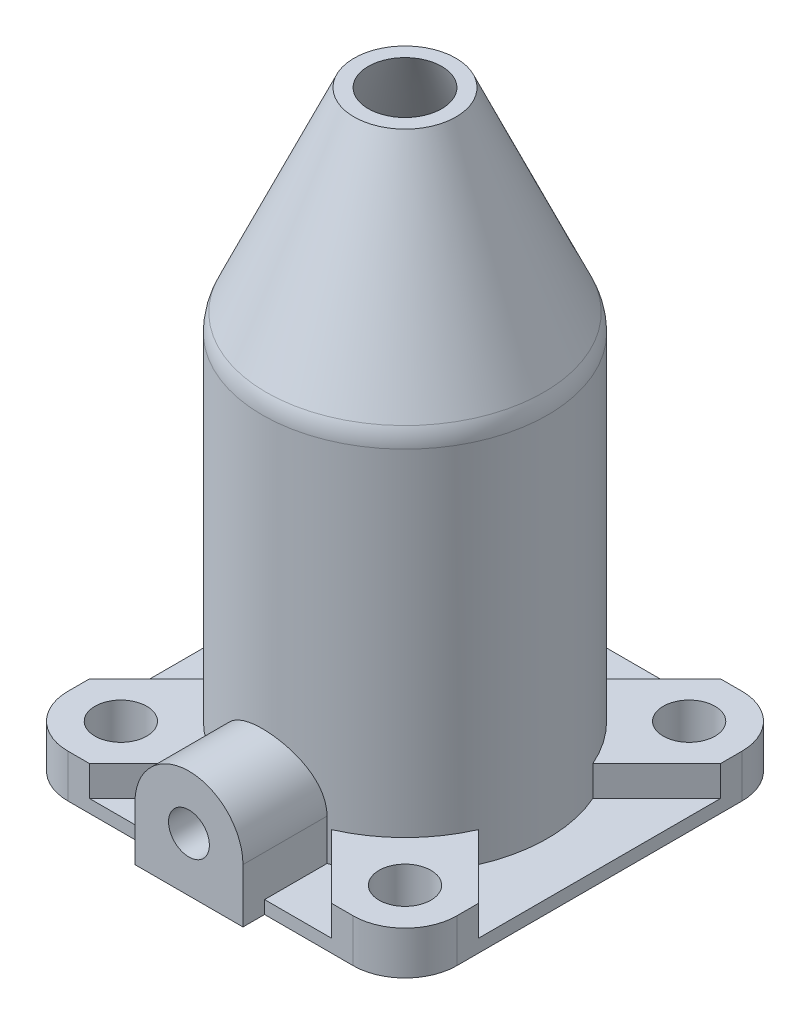
SolidWorks part; units mm, degrees
material "Brass"
ref_plane "Front" through (0, 0, 0) normal (0, 0, 1) x (1, 0, 0)
ref_plane "Top" through (0, 0, 0) normal (0, 1, 0) x (1, 0, 0)
ref_plane "Right" through (0, 0, 0) normal (1, 0, 0) x (0, 0, -1)
sketch "Sketch1" plane through (0, 0, 0) normal (0, 1, 0) x (1, 0, 0)
  line L1 (-33, -45) -> (33, -45)
  line L2 (-45, -33) -> (-45, 33)
  line L3 (-33, 45) -> (33, 45)
  line L4 (45, -33) -> (45, 33)
  line L5 (-45, -45) -> (45, 45) construction
  line L6 (-45, 45) -> (45, -45) construction
  arc A0 (-33, -45) -> (-45, -33) centre (-33, -33) cw
  arc A1 (33, -45) -> (45, -33) centre (33, -33) ccw
  arc A2 (33, 45) -> (45, 33) centre (33, 33) cw
  arc A3 (-45, 33) -> (-33, 45) centre (-33, 33) cw
  point P0 (0, 0)
  dimension "D1" = 12
  dimension "D2" = 12
  dimension "D3" = 12
  dimension "D4" = 12
  dimension "D5" = 90
extrude "Boss-Extrude1" add sketch "Sketch1" along normal blind 3
sketch "Sketch2" plane through (0, 3, 0) normal (0, 1, 0) x (1, 0, 0)
  circle A0 centre (0, 0) radius 30
  dimension "D1" = 60
extrude "Cut-Extrude1" cut sketch "Sketch2" against normal up to surface (3 mm away) up to face at (0, 0, 0)
sketch "Sketch3" plane through (0, 0, 0) normal (0, 0, 1) x (1, 0, 0)
  line L0 (30, 3) -> (30, 89.3545)
  line L1 (-33, 3) -> (33, 3) construction
  line L2 (30, 89.3545) -> (8.5, 137)
  line L3 (8.5, 137) -> (11.7913, 137)
  line L4 (11.7913, 137) -> (33, 90)
  line L5 (33, 90) -> (33, 3)
  line L6 (33, 3) -> (30, 3)
  line L7 (30, 89.3545) -> (32.7345, 90.5884) construction
  line L8 (30, 3) -> (-30, 3) construction
  line L9 (0, -50) -> (0, 50) construction
  line L10 (33, 0) -> (-33, 0) construction
  dimension "D1" = 3
  dimension "D2" = 134
  dimension "D3" = 8.5
  dimension "D4" = 87
  dimension "D5" = 137
  dimension "D6" = 33
revolve "Revolve1" add sketch "Sketch3" angle 360 about axis through (0, -84.8528, 0) along (0, 1, 0)
sketch "Sketch4" plane through (0, 3, 0) normal (0, 1, 0) x (1, 0, 0)
  line L0 (-33, -33) -> (0, 0) construction
  line L1 (-13.2518, -30.2223) -> (-28.0294, -45)
  line L2 (-33, -45) -> (33, -45) construction
  line L3 (-30.2223, -13.2518) -> (-45, -28.0294)
  line L4 (-45, 33) -> (-45, -33) construction
  line L5 (-33, -45) -> (-28.0294, -45)
  line L6 (-45, -28.0294) -> (-45, -33)
  circle A1 centre (0, 0) radius 33 construction
  arc A2 (-45, -33) -> (-33, -45) centre (-33, -33) ccw construction
  arc A3 (-45, -33) -> (-33, -45) centre (-33, -33) ccw
  arc A4 (-30.2223, -13.2518) -> (-13.2518, -30.2223) centre (0, 0) ccw
  dimension "D1" = 24
extrude "Boss-Extrude2" add sketch "Sketch4" along normal blind 7
sketch "Sketch5" plane through (0, 10, 0) normal (0, 1, 0) x (1, 0, 0)
  line L0 (-41.4853, -41.4853) -> (-23.3345, -23.3345) construction
  circle A0 centre (-32.8805, -32.8805) radius 6
  arc A1 (-45, -33) -> (-33, -45) centre (-33, -33) ccw construction
  arc A2 (-30.2223, -13.2518) -> (-13.2518, -30.2223) centre (0, 0) ccw construction
  dimension "D1" = 12
  dimension "D2" = 46.5
extrude "Cut-Extrude2" cut sketch "Sketch5" against normal up to surface (10 mm away) up to face at (0, 0, -30)
pattern_circular "CirPattern1" count 4 over 360 about axis through (0, 0, 0) along (0, 1, 0) of "Boss-Extrude2", "Cut-Extrude2"
sketch "Sketch6" plane through (0, 0, 45) normal (0, 0, 1) x (1, 0, 0)
  line L1 (0, -50) -> (0, 50) construction
  line L3 (-12.5, 12.5) -> (-12.5, 0)
  line L4 (-12.5, 0) -> (12.5, 0)
  line L5 (12.5, 12.5) -> (12.5, 0)
  line L6 (-3.1148, 24.6057) -> (12.5, 0) construction
  line L8 (-12.5, 0) -> (3.1148, 24.6057) construction
  line L9 (50, 0) -> (-50, 0) construction
  arc A0 (12.5, 12.5) -> (-12.5, 12.5) centre (0, 12.5) ccw
  point P0 (0, 19.6975)
  point P4 (0, 25)
  dimension "D2" = 25
  dimension "D1" = 25
extrude "Boss-Extrude3" add sketch "Sketch6" against normal up to body from offset 5 separate body
sketch "Sketch8" plane through (0, 0, 50) normal (0, 0, 1) x (1, 0, 0)
  line L0 (50, 0) -> (-50, 0) construction
  circle A0 centre (0, 12.5) radius 4.725
  dimension "D1" = 9.45
  dimension "D2" = 12.5
extrude "Cut-Extrude3" cut sketch "Sketch8" against normal blind 18 contours A0
sketch "Sketch9" plane through (0, 0, 50) normal (0, 0, 1) x (1, 0, 0)
  line L3 (12.5, 0) -> (12.5, 12.5)
  line L4 (-12.5, 12.5) -> (-12.5, 0)
  line L5 (-12.5, 0) -> (12.5, 0)
  line L6 (12.5, 0) -> (12.5, 12.5)
  line L7 (-12.5, 12.5) -> (-12.5, 0)
  line L8 (-12.5, 0) -> (12.5, 0)
  arc A1 (12.5, 12.5) -> (-12.5, 12.5) centre (0, 12.5) ccw
  arc A2 (12.5, 12.5) -> (-12.5, 12.5) centre (0, 12.5) ccw
  circle A3 centre (0, 12.5) radius 4.725 construction
  circle A4 centre (0, 12.5) radius 4.725
  dimension "D1" = 0
extrude "Boss-Extrude4" [suppressed] add sketch "Sketch9" along normal blind 1.5 separate body
sketch "Sketch10" plane through (0, 10, 0) normal (0, 1, 0) x (1, 0, 0)
  line L4 (-13.2518, 30.2223) -> (-28.0294, 45)
  line L5 (-28.0294, 45) -> (-33, 45)
  line L6 (-45, 33) -> (-45, 28.0294)
  line L7 (-45, 28.0294) -> (-30.2223, 13.2518)
  line L8 (-13.2518, 30.2223) -> (-28.0294, 45)
  line L9 (-28.0294, 45) -> (-33, 45)
  line L10 (-45, 33) -> (-45, 28.0294)
  line L11 (-45, 28.0294) -> (-30.2223, 13.2518)
  line L12 (30.2223, 13.2518) -> (45, 28.0294)
  line L13 (45, 28.0294) -> (45, 33)
  line L14 (33, 45) -> (28.0294, 45)
  line L15 (28.0294, 45) -> (13.2518, 30.2223)
  line L16 (30.2223, 13.2518) -> (45, 28.0294)
  line L17 (45, 28.0294) -> (45, 33)
  line L18 (33, 45) -> (28.0294, 45)
  line L19 (28.0294, 45) -> (13.2518, 30.2223)
  line L20 (13.2518, -30.2223) -> (28.0294, -45)
  line L21 (28.0294, -45) -> (33, -45)
  line L22 (45, -33) -> (45, -28.0294)
  line L23 (45, -28.0294) -> (30.2223, -13.2518)
  line L24 (13.2518, -30.2223) -> (28.0294, -45)
  line L25 (28.0294, -45) -> (33, -45)
  line L26 (45, -33) -> (45, -28.0294)
  line L27 (45, -28.0294) -> (30.2223, -13.2518)
  line L28 (-30.2223, -13.2518) -> (-45, -28.0294)
  line L29 (-45, -28.0294) -> (-45, -33)
  line L30 (-33, -45) -> (-28.0294, -45)
  line L31 (-28.0294, -45) -> (-13.2518, -30.2223)
  line L32 (-30.2223, -13.2518) -> (-45, -28.0294)
  line L33 (-45, -28.0294) -> (-45, -33)
  line L34 (-33, -45) -> (-28.0294, -45)
  line L35 (-28.0294, -45) -> (-13.2518, -30.2223)
  circle A0 centre (32.8805, 32.8805) radius 6 construction
  circle A1 centre (32.8805, -32.8805) radius 6 construction
  arc A2 (-13.2518, 30.2223) -> (-30.2223, 13.2518) centre (0, 0) ccw
  arc A3 (-33, 45) -> (-45, 33) centre (-33, 33) ccw
  arc A4 (-13.2518, 30.2223) -> (-30.2223, 13.2518) centre (0, 0) ccw
  arc A5 (-33, 45) -> (-45, 33) centre (-33, 33) ccw
  circle A6 centre (-32.8805, -32.8805) radius 6 construction
  circle A7 centre (-32.8805, 32.8805) radius 6 construction
  circle A8 centre (32.8805, 32.8805) radius 6
  circle A9 centre (32.8805, -32.8805) radius 6
  circle A10 centre (-32.8805, -32.8805) radius 6
  circle A11 centre (-32.8805, 32.8805) radius 6
  arc A14 (30.2223, 13.2518) -> (13.2518, 30.2223) centre (0, 0) ccw
  arc A15 (45, 33) -> (33, 45) centre (33, 33) ccw
  arc A16 (30.2223, 13.2518) -> (13.2518, 30.2223) centre (0, 0) ccw
  arc A17 (45, 33) -> (33, 45) centre (33, 33) ccw
  arc A18 (13.2518, -30.2223) -> (30.2223, -13.2518) centre (0, 0) ccw
  arc A19 (33, -45) -> (45, -33) centre (33, -33) ccw
  arc A20 (13.2518, -30.2223) -> (30.2223, -13.2518) centre (0, 0) ccw
  arc A21 (33, -45) -> (45, -33) centre (33, -33) ccw
  arc A22 (-30.2223, -13.2518) -> (-13.2518, -30.2223) centre (0, 0) ccw
  arc A23 (-45, -33) -> (-33, -45) centre (-33, -33) ccw
  arc A24 (-30.2223, -13.2518) -> (-13.2518, -30.2223) centre (0, 0) ccw
  arc A25 (-45, -33) -> (-33, -45) centre (-33, -33) ccw
  dimension "D1" = 0
  dimension "D2" = 0
  dimension "D3" = 0
  dimension "D4" = 0
extrude "Boss-Extrude5" [suppressed] add sketch "Sketch10" along normal blind 1.5 separate body
sketch "Sketch11" plane through (0, 0, 0) normal (0, -1, 0) x (1, 0, 0)
  line L8 (-45, 33) -> (-45, -33)
  line L9 (-33, -45) -> (33, -45)
  line L10 (45, -33) -> (45, 33)
  line L11 (33, 45) -> (12.5, 45)
  line L12 (12.5, 45) -> (12.5, 50)
  line L13 (12.5, 50) -> (-12.5, 50)
  line L14 (-12.5, 50) -> (-12.5, 45)
  line L15 (-12.5, 45) -> (-33, 45)
  line L16 (-45, 33) -> (-45, -33)
  line L17 (-33, -45) -> (33, -45)
  line L18 (45, -33) -> (45, 33)
  line L19 (33, 45) -> (12.5, 45)
  line L20 (12.5, 45) -> (12.5, 50)
  line L21 (12.5, 50) -> (-12.5, 50)
  line L22 (-12.5, 50) -> (-12.5, 45)
  line L23 (-12.5, 45) -> (-33, 45)
  circle A0 centre (32.8805, -32.8805) radius 6 construction
  circle A1 centre (32.8805, 32.8805) radius 6 construction
  circle A2 centre (0, 0) radius 30 construction
  circle A3 centre (-32.8805, -32.8805) radius 6 construction
  arc A4 (-33, 45) -> (-45, 33) centre (-33, 33) ccw
  arc A5 (-45, -33) -> (-33, -45) centre (-33, -33) ccw
  arc A6 (33, -45) -> (45, -33) centre (33, -33) ccw
  arc A7 (45, 33) -> (33, 45) centre (33, 33) ccw
  arc A8 (-33, 45) -> (-45, 33) centre (-33, 33) ccw
  arc A9 (-45, -33) -> (-33, -45) centre (-33, -33) ccw
  arc A10 (33, -45) -> (45, -33) centre (33, -33) ccw
  arc A11 (45, 33) -> (33, 45) centre (33, 33) ccw
  circle A12 centre (-32.8805, 32.8805) radius 6 construction
  circle A13 centre (32.8805, -32.8805) radius 6
  circle A14 centre (32.8805, 32.8805) radius 6
  circle A15 centre (0, 0) radius 30
  circle A16 centre (-32.8805, -32.8805) radius 6
  circle A17 centre (-32.8805, 32.8805) radius 6
  dimension "D1" = 0
extrude "Boss-Extrude6" [suppressed] add sketch "Sketch11" along normal blind 1.5 separate body
fillet "Fillet1" radius 10 1 edges at (0, 90, -33)
fillet "Fillet2" [suppressed] radius 1
